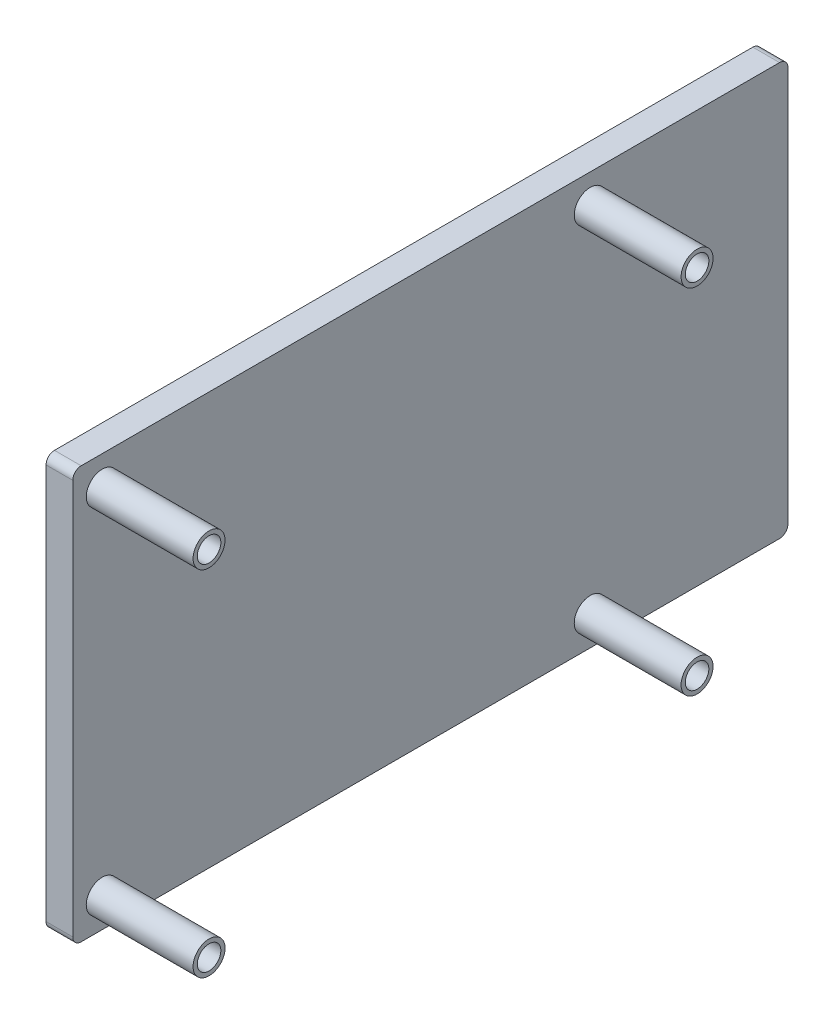
SolidWorks part; units mm, degrees
ref_plane "Front" through (0, 0, 0) normal (0, 0, 1) x (1, 0, 0)
ref_plane "Top" through (0, 0, 0) normal (0, 1, 0) x (1, 0, 0)
ref_plane "Right" through (0, 0, 0) normal (1, 0, 0) x (0, 0, -1)
sketch "Sketch1" plane through (0, 0, 0) normal (1, 0, 0) x (0, 0, -1)
  line L1 (-54.3298, 15.3018) -> (30.6702, 15.3018)
  line L2 (-54.3298, 15.3018) -> (-54.3298, -33.6982)
  line L3 (-54.3298, -33.6982) -> (30.6702, -33.6982)
  line L4 (30.6702, 15.3018) -> (30.6702, -33.6982)
  dimension "D1" = 49
  dimension "D2" = 85
extrude "Boss-Extrude1" add sketch "Sketch1" along normal blind 3.175
sketch "Sketch2" plane through (3.175, 0, 0) normal (1, 0, 0) x (0, 0, -1)
  line L0 (-54.3298, 15.3018) -> (-54.3298, -33.6982) construction
  line L2 (30.6702, 15.3018) -> (-54.3298, 15.3018) construction
  line L3 (-54.3298, -9.1982) -> (30.6702, -9.1982) construction
  line L4 (30.6702, -33.6982) -> (30.6702, 15.3018) construction
  circle A0 centre (-50.8298, 11.8018) radius 1.9
  circle A1 centre (7.1702, 11.8018) radius 1.9
  circle A4 centre (-50.8298, 11.8018) radius 1.4
  circle A5 centre (7.1702, 11.8018) radius 1.4
  circle A6 centre (7.1702, -30.1982) radius 1.4
  circle A7 centre (7.1702, -30.1982) radius 1.9
  circle A8 centre (-50.8298, -30.1982) radius 1.4
  circle A9 centre (-50.8298, -30.1982) radius 1.9
  dimension "D3" = 3.8
  dimension "D4" = 2.8
  dimension "D7" = 3.8
  dimension "D8" = 2.8
  dimension "D1" = 3.5
  dimension "D2" = 3.5
  dimension "D5" = 58
  dimension "D6" = 3.5
extrude "Boss-Extrude2" add sketch "Sketch2" along normal blind 12.7
fillet "Fillet1" radius 1 4 edges at (1.5875, 15.3018, 54.3298) (1.5875, 15.3018, -30.6702) (1.5875, -33.6982, -30.6702) (1.5875, -33.6982, 54.3298)
